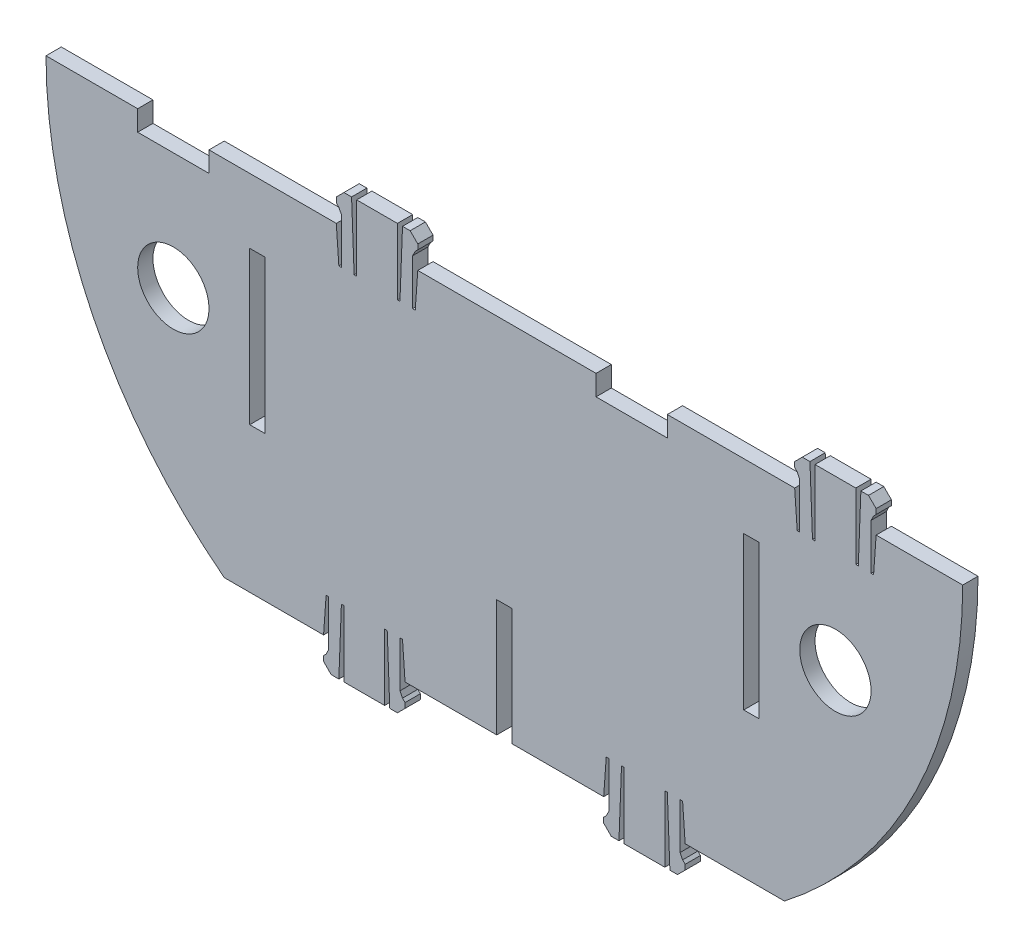
SolidWorks part; units mm, degrees
ref_plane "Front Plane" through (0, 0, 0) normal (0, 0, 1) x (1, 0, 0)
ref_plane "Top Plane" through (0, 0, 0) normal (0, 1, 0) x (1, 0, 0)
ref_plane "Right Plane" through (0, 0, 0) normal (1, 0, 0) x (0, 0, -1)
sketch "Sketch1" plane through (0, 0, 0) normal (0, 0, 1) x (1, 0, 0)
  line L0 (-55, -71.239) -> (-35.5, -71.239)
  line L1 (-90, 0) -> (-72, 0)
  line L2 (32, 0) -> (57, 0)
  line L3 (18, -4) -> (32, -4)
  line L4 (18, -4) -> (18, 0)
  line L5 (18, 0) -> (-17, 0)
  line L6 (32, -4) -> (32, 0)
  line L7 (57, 0) -> (57.5, -7.0022)
  line L8 (57.5, -7.0022) -> (58, -7.0022)
  line L9 (-72, -4) -> (-58, -4)
  line L10 (-72, -4) -> (-72, 0)
  line L11 (-58, 0) -> (-33, 0)
  line L12 (73, 0) -> (90, 0)
  line L13 (-58, -4) -> (-58, 0)
  line L14 (58, -7.0022) -> (58, 1.9978)
  line L15 (58, 1.9978) -> (57.5, 2.9978)
  line L16 (55, -71.239) -> (35.5, -71.239)
  line L17 (-19.5, -71.239) -> (19.5, -71.239)
  line L18 (-19.5, -71.239) -> (-20, -64.2369)
  line L19 (-1.5, -35.24) -> (1.5, -35.24)
  line L20 (-1.5, -35.24) -> (-1.5, -71.24)
  line L21 (-17.7638, -71.239) -> (6.9745, -71.239)
  line L22 (-1.5, -71.24) -> (1.5, -71.24)
  line L23 (1.5, -35.24) -> (1.5, -71.24)
  line L24 (-1.5, -35.24) -> (1.5, -71.24) construction
  line L25 (-1.5, -71.24) -> (1.5, -35.24) construction
  line L26 (-20, -64.2369) -> (-20.5, -64.2369)
  line L27 (-20.5, -64.2369) -> (-20.5, -73.2369)
  line L28 (-20.5, -73.2369) -> (-20, -74.2369)
  line L29 (-20, -74.2369) -> (-19.5, -74.7369)
  line L30 (-19.5, -74.7369) -> (-19.5, -75.7369)
  line L31 (-19.5, -75.7369) -> (-21, -77.2369)
  line L32 (-21, -77.2369) -> (-22.5, -77.2369)
  line L33 (-22.5, -77.2369) -> (-23, -64.2369)
  line L34 (-23, -64.2369) -> (-23.5, -64.2369)
  line L35 (-23.5, -64.2369) -> (-23.5, -77.2369)
  line L36 (-27.5, -71.239) -> (-27.5, -76.9776) construction
  line L37 (-31.5, -64.2369) -> (-31.5, -77.2369)
  line L38 (-32, -64.2369) -> (-31.5, -64.2369)
  line L39 (-32.5, -77.2369) -> (-32, -64.2369)
  line L40 (-34, -77.2369) -> (-32.5, -77.2369)
  line L41 (-35.5, -75.7369) -> (-34, -77.2369)
  line L42 (-35.5, -74.7369) -> (-35.5, -75.7369)
  line L43 (-35, -74.2369) -> (-35.5, -74.7369)
  line L44 (-34.5, -73.2369) -> (-35, -74.2369)
  line L45 (-34.5, -64.2369) -> (-34.5, -73.2369)
  line L46 (-35, -64.2369) -> (-34.5, -64.2369)
  line L47 (-35.5, -71.239) -> (-35, -64.2369)
  line L48 (-23.5, -77.2369) -> (-31.5, -77.2369)
  line L49 (-33, 0) -> (-32.5, -7.0022)
  line L50 (-32.5, -7.0022) -> (-32, -7.0022)
  line L51 (-32, -7.0022) -> (-32, 1.9978)
  line L52 (-32, 1.9978) -> (-32.5, 2.9978)
  line L53 (-32.5, 2.9978) -> (-33, 3.4978)
  line L54 (-33, 3.4978) -> (-33, 4.4978)
  line L55 (-33, 4.4978) -> (-31.5, 5.9978)
  line L56 (-31.5, 5.9978) -> (-30, 5.9978)
  line L57 (-30, 5.9978) -> (-29.5, -7.0022)
  line L58 (-29.5, -7.0022) -> (-29, -7.0022)
  line L59 (-29, -7.0022) -> (-29, 5.9978)
  line L60 (-25, 0) -> (-25, 5.7386) construction
  line L61 (-21, -7.0022) -> (-21, 5.9978)
  line L62 (-20.5, -7.0022) -> (-21, -7.0022)
  line L63 (-20, 5.9978) -> (-20.5, -7.0022)
  line L64 (-18.5, 5.9978) -> (-20, 5.9978)
  line L65 (-17, 4.4978) -> (-18.5, 5.9978)
  line L66 (-17, 3.4978) -> (-17, 4.4978)
  line L67 (-17.5, 2.9978) -> (-17, 3.4978)
  line L68 (-18, 1.9978) -> (-17.5, 2.9978)
  line L69 (-18, -7.0022) -> (-18, 1.9978)
  line L70 (-17.5, -7.0022) -> (-18, -7.0022)
  line L71 (-17, 0) -> (-17.5, -7.0022)
  line L72 (-29, 5.9978) -> (-21, 5.9978)
  line L73 (57.5, 2.9978) -> (57, 3.4978)
  line L74 (57, 3.4978) -> (57, 4.4978)
  line L75 (57, 4.4978) -> (58.5, 5.9978)
  line L76 (58.5, 5.9978) -> (60, 5.9978)
  line L77 (60, 5.9978) -> (60.5, -7.0022)
  line L78 (60.5, -7.0022) -> (61, -7.0022)
  line L79 (61, -7.0022) -> (61, 5.9978)
  line L80 (65, 0) -> (65, 5.7386) construction
  line L81 (69, -7.0022) -> (69, 5.9978)
  line L82 (69.5, -7.0022) -> (69, -7.0022)
  line L83 (70, 5.9978) -> (69.5, -7.0022)
  line L84 (71.5, 5.9978) -> (70, 5.9978)
  line L85 (73, 4.4978) -> (71.5, 5.9978)
  line L86 (73, 3.4978) -> (73, 4.4978)
  line L87 (72.5, 2.9978) -> (73, 3.4978)
  line L88 (72, 1.9978) -> (72.5, 2.9978)
  line L89 (72, -7.0022) -> (72, 1.9978)
  line L90 (72.5, -7.0022) -> (72, -7.0022)
  line L91 (73, 0) -> (72.5, -7.0022)
  line L92 (61, 5.9978) -> (69, 5.9978)
  line L93 (35.5, -71.239) -> (35, -64.2369)
  line L94 (35, -64.2369) -> (34.5, -64.2369)
  line L95 (34.5, -64.2369) -> (34.5, -73.2369)
  line L96 (34.5, -73.2369) -> (35, -74.2369)
  line L97 (35, -74.2369) -> (35.5, -74.7369)
  line L98 (35.5, -74.7369) -> (35.5, -75.7369)
  line L99 (35.5, -75.7369) -> (34, -77.2369)
  line L100 (34, -77.2369) -> (32.5, -77.2369)
  line L101 (32.5, -77.2369) -> (32, -64.2369)
  line L102 (32, -64.2369) -> (31.5, -64.2369)
  line L103 (31.5, -64.2369) -> (31.5, -77.2369)
  line L104 (27.5, -71.239) -> (27.5, -76.9776) construction
  line L105 (23.5, -64.2369) -> (23.5, -77.2369)
  line L106 (23, -64.2369) -> (23.5, -64.2369)
  line L107 (22.5, -77.2369) -> (23, -64.2369)
  line L108 (21, -77.2369) -> (22.5, -77.2369)
  line L109 (19.5, -75.7369) -> (21, -77.2369)
  line L110 (19.5, -74.7369) -> (19.5, -75.7369)
  line L111 (20, -74.2369) -> (19.5, -74.7369)
  line L112 (20.5, -73.2369) -> (20, -74.2369)
  line L113 (20.5, -64.2369) -> (20.5, -73.2369)
  line L114 (20, -64.2369) -> (20.5, -64.2369)
  line L115 (19.5, -71.239) -> (20, -64.2369)
  line L116 (31.5, -77.2369) -> (23.5, -77.2369)
  arc A0 (-90, 0) -> (-55, -71.239) centre (0, 0) ccw
  arc A1 (55, -71.239) -> (90, 0) centre (0, 0) ccw
  point P10 (0, -53.24)
  point P32 (65, 0)
  point P33 (57, 0)
  point P34 (73, 0)
  point P35 (73, 0)
  point P36 (-27.5, -71.239)
  point P37 (-19.5, -71.239)
  point P38 (-35.5, -71.239)
  point P39 (-35.5, -71.239)
  point P66 (-25, 0)
  point P67 (-33, 0)
  point P68 (-17, 0)
  point P69 (-17, 0)
  point P116 (27.5, -71.239)
  point P117 (35.5, -71.239)
  point P118 (19.5, -71.239)
  point P119 (19.5, -71.239)
  dimension "D1" = 180
  dimension "D2" = 110
  dimension "D3" = 14
  dimension "D4" = 14
  dimension "D5" = 4
  dimension "D6" = 35
  dimension "D7" = 25
  dimension "D8" = 19.5
  dimension "D9" = 19.5
  dimension "D10" = 39
  dimension "D11" = 36
  dimension "D12" = 3
  dimension "D13" = 8
  dimension "D14" = 0.5
  dimension "D15" = 9
  dimension "D16" = 0.5
  dimension "D17" = 1
  dimension "D18" = 0.5
  dimension "D19" = 0.5
  dimension "D20" = 1
  dimension "D21" = 1.5
  dimension "D22" = 1.5
  dimension "D23" = 0.5
  dimension "D24" = 0.5
  dimension "D25" = 13
  dimension "D26" = 7.0022
  dimension "D27" = 0.5
  dimension "D28" = 8
  dimension "D29" = 0.5
  dimension "D30" = 9
  dimension "D31" = 0.5
  dimension "D32" = 1
  dimension "D33" = 0.5
  dimension "D34" = 0.5
  dimension "D35" = 1
  dimension "D36" = 1.5
  dimension "D37" = 1.5
  dimension "D38" = 0.5
  dimension "D39" = 0.5
  dimension "D40" = 13
  dimension "D41" = 7.0022
  dimension "D42" = 0.5
  dimension "D43" = 4
  dimension "D44" = 18
  dimension "D45" = 25
  dimension "D46" = 17
  dimension "D47" = 1.5
  dimension "D48" = 13
  dimension "D49" = 1.5
  dimension "D50" = 0.5
  dimension "D51" = 9
  dimension "D52" = 0.5
  dimension "D53" = 1
  dimension "D54" = 0.5
  dimension "D55" = 0.5
  dimension "D56" = 1
  dimension "D57" = 1.5
  dimension "D58" = 1.5
  dimension "D59" = 0.5
  dimension "D60" = 0.5
  dimension "D61" = 13
  dimension "D62" = 7.0022
  dimension "D63" = 0.5
  dimension "D64" = 1.5
  dimension "D65" = 0.5
  dimension "D66" = 9
  dimension "D67" = 0.5
  dimension "D68" = 1
  dimension "D69" = 0.5
  dimension "D70" = 0.5
  dimension "D71" = 1
  dimension "D72" = 1.5
  dimension "D73" = 1.5
  dimension "D74" = 0.5
  dimension "D75" = 0.5
  dimension "D76" = 13
  dimension "D77" = 7.0022
  dimension "D78" = 0.5
  dimension "D79" = 1.5
  dimension "D80" = 13
  dimension "D81" = 13
  dimension "D82" = 13
extrude "Boss-Extrude1" add sketch "Sketch1" along normal blind 3 contours A0 L0 L47 L46 L45 L44 L43 L42 L41 L40 L39 L38 L37 L48 L35 L34 L33 L32 L31 L30 L29 L28 L27 L26 L18 L17 L115 L114 L113 L112 L111 L110 L109 L108 L107 L106 L105 L116 L103 L102 L101 L100 L99 L98 L97 L96 L95 L94 L93 L16 A1 L12 L91 L90 L89 L88 L87 L86 L85 L84 L83 L82 L81 L92 L79 L78 L77 L76 L75 L74 L73 L15 L14 L8 L7 L2 L6 L3 L4 L5 L71 L70 L69 L68 L67 L66 L65 L64 L63 L62 L61 L72 L59 L58 L57 L56 L55 L54 L53 L52 L51 L50 L49 L11 L13 L9 L10 L1
sketch "Sketch5" plane through (0, 0, 0) normal (0, 0, -1) x (-1, 0, 0)
  line L0 (0, 0) -> (0, -71.239) construction
  line L1 (19.5, -71.239) -> (-19.5, -71.239) construction
  line L2 (-47, -12.74) -> (-47, -42.74)
  line L3 (47, -12.74) -> (47, -42.74)
  line L4 (-47, -12.74) -> (-50, -12.74)
  line L5 (47, -12.74) -> (50, -12.74)
  line L6 (-47, -42.74) -> (-50, -42.74)
  line L7 (47, -42.74) -> (50, -42.74)
  line L8 (-50, -42.74) -> (-50, -12.74)
  line L9 (50, -42.74) -> (50, -12.74)
  dimension "D1" = 30
  dimension "D2" = 3
  dimension "D3" = 47
  dimension "D4" = 12.74
extrude "Cut-Extrude3" cut sketch "Sketch5" against normal blind 3
sketch "Sketch7" plane through (0, 0, 0) normal (0, 0, -1) x (-1, 0, 0)
  line L0 (0, 0) -> (0, -71.239) construction
  line L1 (19.5, -71.239) -> (-19.5, -71.239) construction
  circle A0 centre (65, -27) radius 7
  circle A1 centre (-65, -27) radius 7
  dimension "D1" = 130
  dimension "D2" = 14
  dimension "D3" = 27
extrude "Cut-Extrude4" cut sketch "Sketch7" against normal blind 3
sketch "Sketch8" plane through (0, 0, 0) normal (0, 0, -1) x (-1, 0, 0)
  line L0 (-1.5, -71.239) -> (-1.5, -48.239)
  line L1 (19.5, -71.239) -> (-19.5, -71.239) construction
  line L2 (-1.5, -48.239) -> (1.5, -48.239)
  line L3 (1.5, -48.239) -> (1.5, -71.239)
  point P4 (0, 0)
  dimension "D1" = 23
  dimension "D2" = 3
  dimension "D3" = 1.5
sketch "Sketch9" plane through (0, 0, 0) normal (0, 0, -1) x (-1, 0, 0)
  text T0 "HY1a\r\n" font "Century Gothic" height in points 22
  dimension "D1" = 10
  dimension "D2" = 11
extrude "Cut-Extrude6" cut sketch "Sketch8" against normal blind 3 and the other way through all flip side to cut
